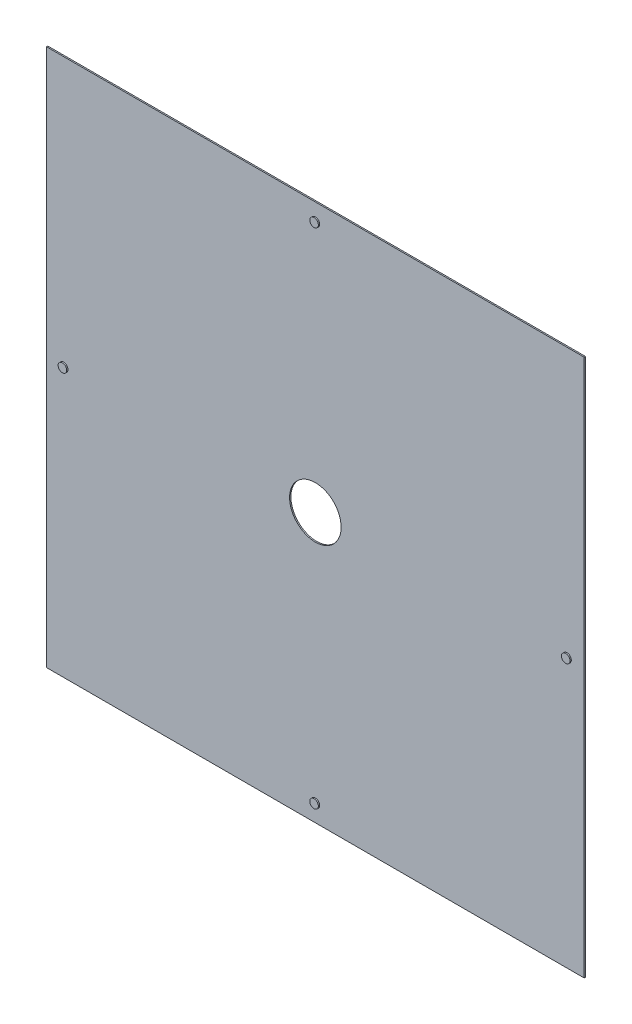
SolidWorks part; units mm, degrees
ref_plane "Front" through (0, 0, 0) normal (0, 0, 1) x (1, 0, 0)
ref_plane "Top" through (0, 0, 0) normal (0, 1, 0) x (1, 0, 0)
ref_plane "Right" through (0, 0, 0) normal (1, 0, 0) x (0, 0, -1)
sketch "Sketch2" plane through (0, 0, 0) normal (0, 0, 1) x (1, 0, 0)
  line L1 (-313, 313) -> (313, 313)
  line L2 (-313, 313) -> (-313, -313)
  line L3 (-313, -313) -> (313, -313)
  line L4 (313, 313) -> (313, -313)
  line L5 (-313, 313) -> (313, -313) construction
  line L6 (-313, -313) -> (313, 313) construction
  circle A0 centre (0, 0) radius 30
  point P0 (0, 0)
  dimension "D3" = 60
  dimension "D1" = 626
  dimension "D2" = 626
extrude "Boss-Extrude1" add sketch "Sketch2" along normal blind 1.5
sketch "Sketch3" plane through (0, 0, 1.5) normal (0, 0, 1) x (1, 0, 0)
  line L0 (-64.0866, 0) -> (74.0741, 0) construction
  line L1 (0, 80.7324) -> (0, -70.7449) construction
  line L2 (313, 313) -> (-313, 313) construction
  line L4 (-313, 313) -> (-313, -313) construction
  circle A0 centre (0, 293) radius 5
  circle A1 centre (-293, 0) radius 5
  circle A2 centre (0, -293) radius 5
  circle A3 centre (293, 0) radius 5
  dimension "D1" = 10
  dimension "D4" = 10
  dimension "D2" = 20
  dimension "D3" = 0
  dimension "D5" = 20
  dimension "D6" = 0
extrude "Boss-Extrude2" add sketch "Sketch3" along normal blind 1.5
